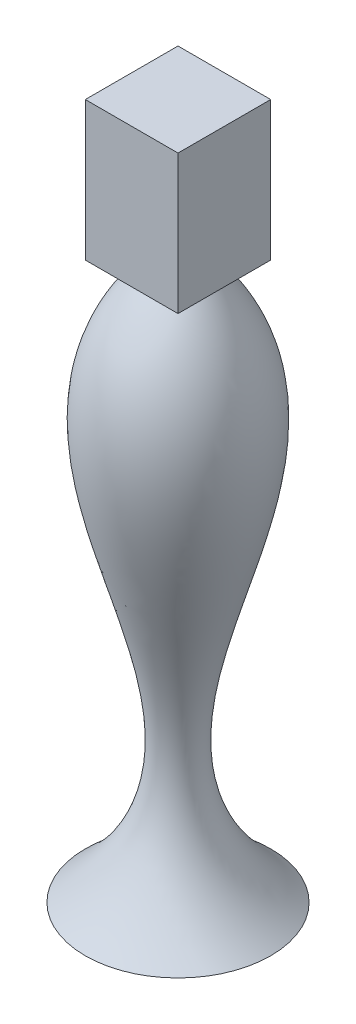
SolidWorks part; units mm, degrees
ref_plane "Front Plane" through (0, 0, 0) normal (0, 0, 1) x (1, 0, 0)
ref_plane "Top Plane" through (0, 0, 0) normal (0, 1, 0) x (1, 0, 0)
ref_plane "Right Plane" through (0, 0, 0) normal (1, 0, 0) x (0, 0, -1)
sketch "Sketch1" plane through (0, 0, 0) normal (0, 0, 1) x (1, 0, 0)
  line L0 (0, 0) -> (0, 457.2) construction
  line L2 (0, 0) -> (0, -152.4)
  line L3 (0, 457.2) -> (-25.4, 457.2)
  line L4 (0, 457.2) -> (0, 0)
  line L5 (0, -152.4) -> (-101.6, -152.4)
  spline S1 degree 3 poles (-101.6, -152.4) (112.2337, 26.0741) (-211.8076, 256.7436) (-25.4, 457.2) knots 0 0 0 0 1 1 1 1
  dimension "D1" = 457.2
  dimension "D3" = 152.4
  dimension "D4" = 101.6
revolve "Revolve3" add sketch "Sketch1" angle 360 about L0
sketch "Sketch10" plane through (0, 457.2, 0) normal (0, 1, 0) x (1, 0, 0)
  line L1 (-50.8, 50.8) -> (50.8, 50.8)
  line L2 (-50.8, 50.8) -> (-50.8, -50.8)
  line L3 (-50.8, -50.8) -> (50.8, -50.8)
  line L4 (50.8, 50.8) -> (50.8, -50.8)
  circle A0 centre (0, 0) radius 25.4 construction
  dimension "D1" = 101.6
  dimension "D2" = 101.6
  dimension "D3" = 50.8
  dimension "D4" = 50.8
extrude "Boss-Extrude5" add sketch "Sketch10" along normal blind 152.4
